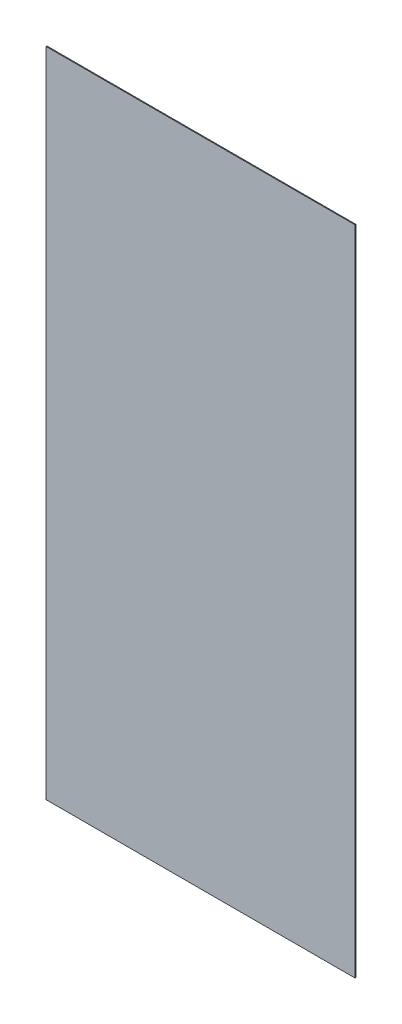
SolidWorks part; units mm, degrees
material "Mahogany"
ref_plane "Front Plane" through (0, 0, 0) normal (0, 0, 1) x (1, 0, 0)
ref_plane "Top Plane" through (0, 0, 0) normal (0, 1, 0) x (1, 0, 0)
ref_plane "Right Plane" through (0, 0, 0) normal (1, 0, 0) x (0, 0, -1)
sketch "Sketch1" plane through (0, 0, 0) normal (0, 0, 1) x (1, 0, 0)
  line L61 (-1420, 0) -> (0, 0)
  line L62 (-1420, 0) -> (-1420, -3000)
  line L63 (-1420, -3000) -> (0, -3000)
  line L64 (0, 0) -> (0, -3000)
  point P4 (0, 0)
  dimension "D1" = 1420
  dimension "D2" = 3000
extrude "Boss-Extrude4" add sketch "Sketch1" along normal blind 4
